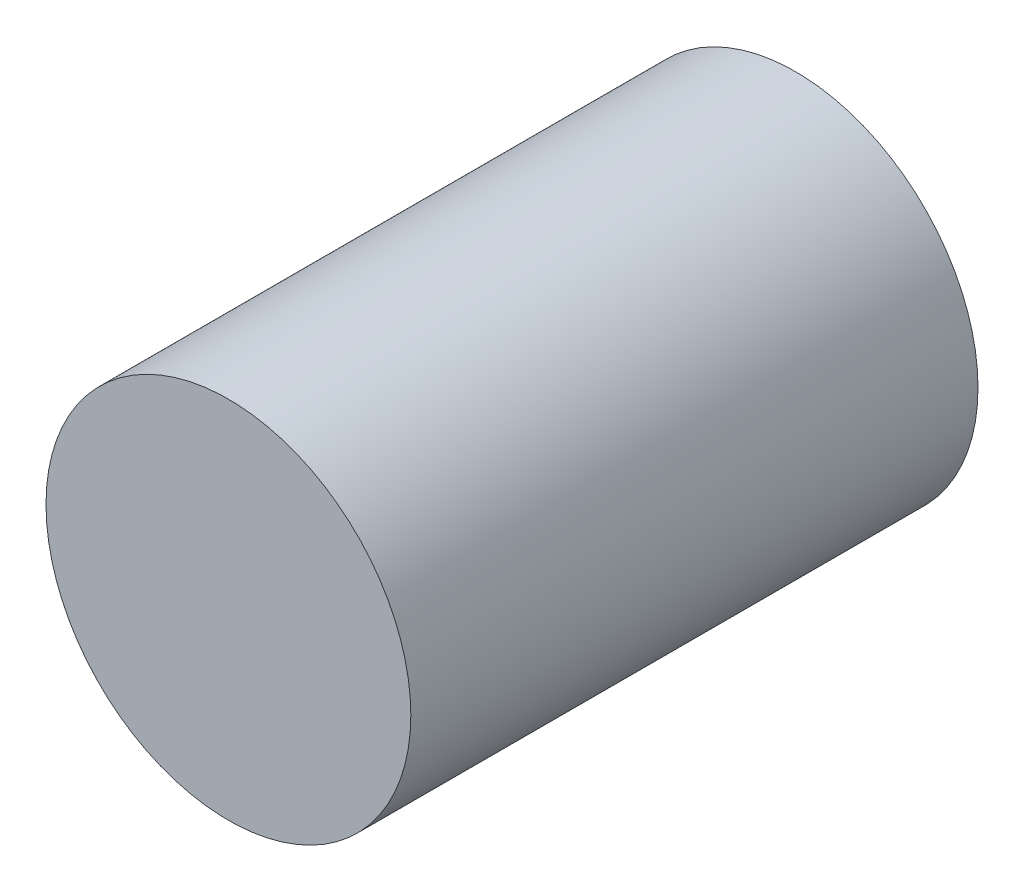
SolidWorks part; units mm, degrees
material "Plain Carbon Steel"
ref_plane "Front Plane" through (0, 0, 0) normal (0, 0, 1) x (1, 0, 0)
ref_plane "Top Plane" through (0, 0, 0) normal (0, 1, 0) x (1, 0, 0)
ref_plane "Right Plane" through (0, 0, 0) normal (1, 0, 0) x (0, 0, -1)
sketch "Sketch1" plane through (0, 0, 0) normal (0, 0, 1) x (1, 0, 0)
  circle A0 centre (0, 0) radius 1.5875
  dimension "D1" = 3.175
extrude "Boss-Extrude1" add sketch "Sketch1" along normal blind 7.62
sketch "Sketch2" plane through (0, 0, 7.62) normal (0, 0, 1) x (1, 0, 0)
  circle A0 centre (0, 0) radius 18.3
  dimension "D1" = 36.6
extrude "Boss-Extrude2" add sketch "Sketch2" along normal blind 56.9
